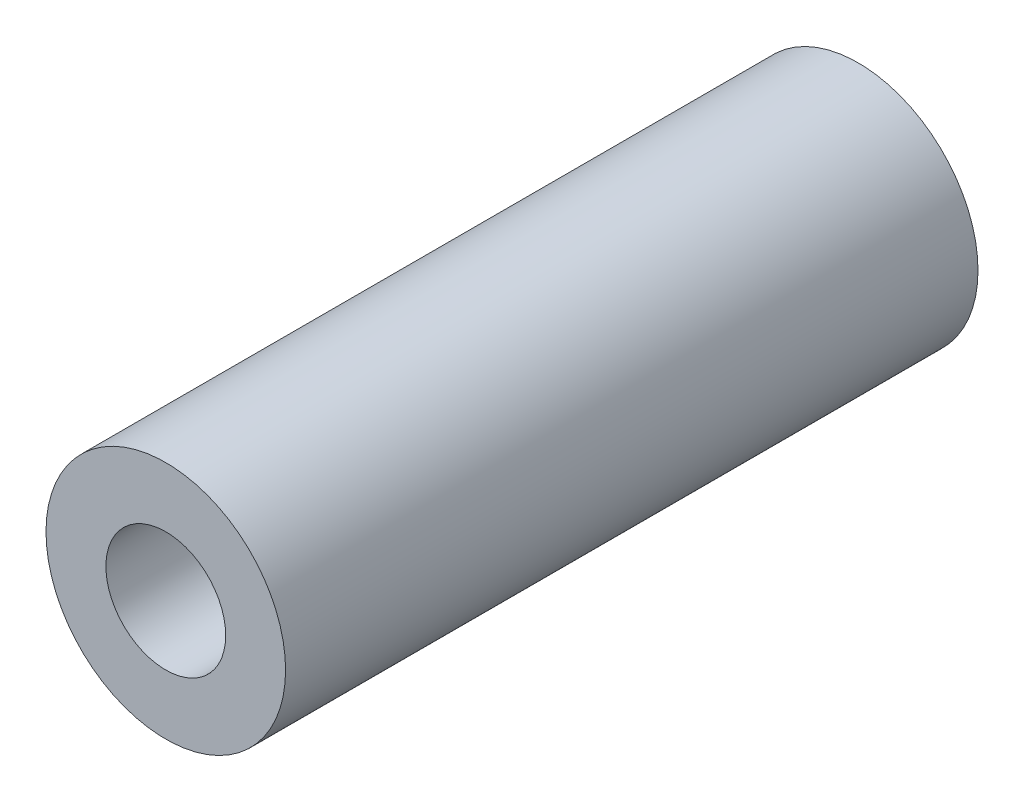
SolidWorks part; units mm, degrees
ref_plane "Front Plane" through (0, 0, 0) normal (0, 0, 1) x (1, 0, 0)
ref_plane "Top Plane" through (0, 0, 0) normal (0, 1, 0) x (1, 0, 0)
ref_plane "Right Plane" through (0, 0, 0) normal (1, 0, 0) x (0, 0, -1)
sketch "Sketch1" plane through (0, 0, 0) normal (0, 0, 1) x (1, 0, 0)
  circle A0 centre (0, 0) radius 5
  dimension "D1" = 10
extrude "Boss-Extrude1" add sketch "Sketch1" along normal blind 28.9
hole_wizard "Ø5.0mm Dowel Hole1" positions "Sketch2" profile "Sketch3" hole size "Ø5.0" standard "ANSI Metric" end condition up to next
sketch "Sketch2" plane through (0, 0, 28.9) normal (0, 0, 1) x (1, 0, 0)
  point P0 (0, 0)
sketch "Sketch3" plane through (0, 0, 28.9) normal (1, 0, 0) x (0, -1, 0)
  line L0 (0, 0) -> (0, 28.9)
  line L1 (0, 28.9) -> (2.5, 28.9)
  line L2 (2.5, 28.9) -> (2.5, 0)
  line L5 (2.5, 0) -> (0, 0)
  line L11 (0, -6.35) -> (0, 107.95) construction
  dimension "Thru Hole Dia." = 5
  dimension "Thru Hole Depth" = 28.9
